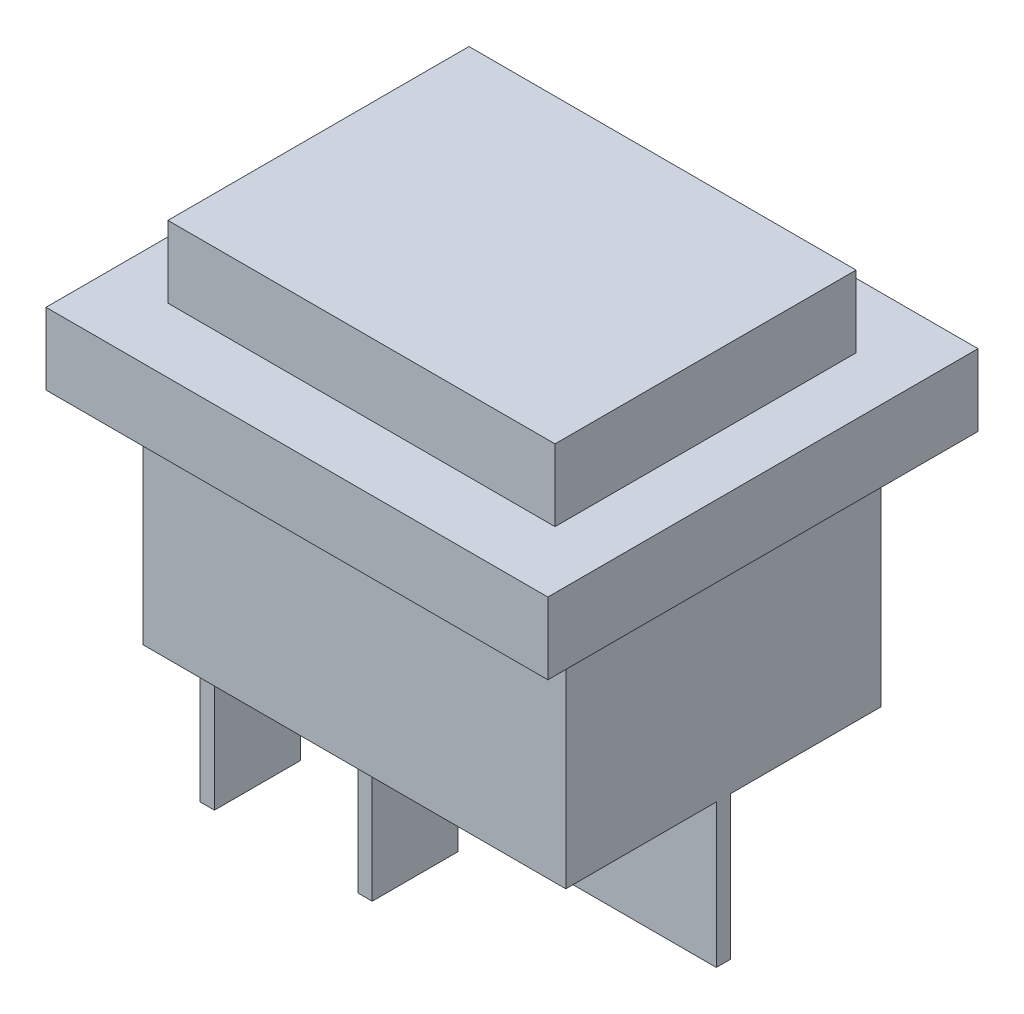
SolidWorks part; units mm, degrees
ref_plane "Спереди" through (0, 0, 0) normal (0, 0, 1) x (1, 0, 0)
ref_plane "Сверху" through (0, 0, 0) normal (0, 1, 0) x (1, 0, 0)
ref_plane "Справа" through (0, 0, 0) normal (1, 0, 0) x (0, 0, -1)
sketch "Эскиз1" plane through (0, 0, 0) normal (0, 1, 0) x (1, 0, 0)
  line L1 (-14.75, 11) -> (14.75, 11)
  line L2 (-14.75, 11) -> (-14.75, -11)
  line L3 (-14.75, -11) -> (14.75, -11)
  line L4 (14.75, 11) -> (14.75, -11)
  line L5 (-14.75, 11) -> (14.75, -11) construction
  line L6 (-14.75, -11) -> (14.75, 11) construction
  point P0 (0, 0)
  dimension "D1" = 22
  dimension "D2" = 29.5
extrude "Бобышка-Вытянуть1" add sketch "Эскиз1" against normal blind 16
sketch "Эскиз2" plane through (0, 0, 0) normal (0, 1, 0) x (1, 0, 0)
  line L1 (-17.5, 15) -> (17.5, 15)
  line L2 (-17.5, 15) -> (-17.5, -15)
  line L3 (-17.5, -15) -> (17.5, -15)
  line L4 (17.5, 15) -> (17.5, -15)
  line L5 (-17.5, 15) -> (17.5, -15) construction
  line L6 (-17.5, -15) -> (17.5, 15) construction
  point P0 (0, 0)
  dimension "D1" = 35
  dimension "D2" = 30
extrude "Бобышка-Вытянуть2" add sketch "Эскиз2" along normal blind 5
sketch "Эскиз3" plane through (0, 5, 0) normal (0, 1, 0) x (1, 0, 0)
  line L1 (-13.5, 10.5) -> (13.5, 10.5)
  line L2 (-13.5, 10.5) -> (-13.5, -10.5)
  line L3 (-13.5, -10.5) -> (13.5, -10.5)
  line L4 (13.5, 10.5) -> (13.5, -10.5)
  line L5 (-13.5, 10.5) -> (13.5, -10.5) construction
  line L6 (-13.5, -10.5) -> (13.5, 10.5) construction
  point P0 (0, 0)
  dimension "D1" = 27
  dimension "D2" = 21
extrude "Бобышка-Вытянуть3" add sketch "Эскиз3" along normal blind 5
sketch "Эскиз4" plane through (0, -16, 0) normal (0, -1, 0) x (1, 0, 0)
  line L0 (14.75, 11) -> (14.75, -11) construction
  line L1 (-14.75, 0.5) -> (14.75, 0.5)
  line L2 (-14.75, 0.5) -> (-14.75, -0.5)
  line L3 (-14.75, -0.5) -> (14.75, -0.5)
  line L4 (14.75, 0.5) -> (14.75, -0.5)
  line L5 (-14.75, 0.5) -> (14.75, -0.5) construction
  line L6 (-14.75, -0.5) -> (14.75, 0.5) construction
  line L7 (-14.75, -11) -> (-14.75, 11) construction
  line L8 (-13.25, 8.5) -> (-12.25, 8.5)
  line L9 (-13.25, 8.5) -> (-13.25, 2.5)
  line L10 (-13.25, 2.5) -> (-12.25, 2.5)
  line L11 (-12.25, 8.5) -> (-12.25, 2.5)
  line L12 (-13.25, 8.5) -> (-12.25, 2.5) construction
  line L13 (-13.25, 2.5) -> (-12.25, 8.5) construction
  line L14 (-2.25, 8.5) -> (-1.25, 8.5)
  line L15 (-2.25, 8.5) -> (-2.25, 2.5)
  line L16 (-2.25, 2.5) -> (-1.25, 2.5)
  line L17 (-1.25, 8.5) -> (-1.25, 2.5)
  line L18 (-2.25, 8.5) -> (-1.25, 2.5) construction
  line L19 (-2.25, 2.5) -> (-1.25, 8.5) construction
  line L20 (-13.25, -2.5) -> (-12.25, -2.5)
  line L21 (-13.25, -2.5) -> (-13.25, -8.5)
  line L22 (-13.25, -8.5) -> (-12.25, -8.5)
  line L23 (-12.25, -2.5) -> (-12.25, -8.5)
  line L24 (-13.25, -2.5) -> (-12.25, -8.5) construction
  line L25 (-13.25, -8.5) -> (-12.25, -2.5) construction
  line L26 (-2.25, -2.5) -> (-1.25, -2.5)
  line L27 (-2.25, -2.5) -> (-2.25, -8.5)
  line L28 (-2.25, -8.5) -> (-1.25, -8.5)
  line L29 (-1.25, -2.5) -> (-1.25, -8.5)
  line L30 (-2.25, -2.5) -> (-1.25, -8.5) construction
  line L31 (-2.25, -8.5) -> (-1.25, -2.5) construction
  point P0 (0, 0)
  point P8 (-12.75, 5.5)
  point P13 (-1.75, 5.5)
  point P18 (-12.75, -5.5)
  point P23 (-1.75, -5.5)
  point P30 (-12.75, -8.5)
  dimension "D1" = 1
  dimension "D2" = 6
  dimension "D3" = 1
  dimension "D4" = 1.5
  dimension "D5" = 10
  dimension "D6" = 9
  dimension "D7" = 9
extrude "Бобышка-Вытянуть4" add sketch "Эскиз4" along normal blind 10
